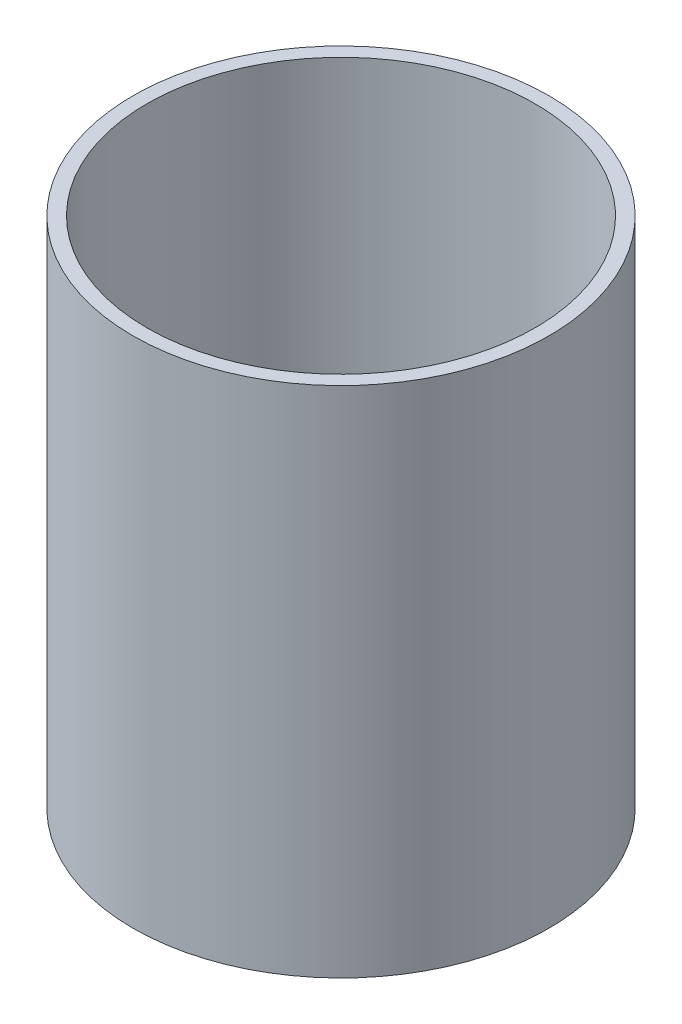
SolidWorks part; units mm, degrees
ref_plane "Front Plane" through (0, 0, 0) normal (0, 0, 1) x (1, 0, 0)
ref_plane "Top Plane" through (0, 0, 0) normal (0, 1, 0) x (1, 0, 0)
ref_plane "Right Plane" through (0, 0, 0) normal (1, 0, 0) x (0, 0, -1)
sketch "Sketch1" plane through (0, 0, 0) normal (0, 1, 0) x (1, 0, 0)
  circle A0 centre (0, 0) radius 14
  circle A1 centre (0, 0) radius 15
  dimension "D1" = 30
  dimension "D2" = 28
extrude "Boss-Extrude1" add sketch "Sketch1" along normal blind 37
